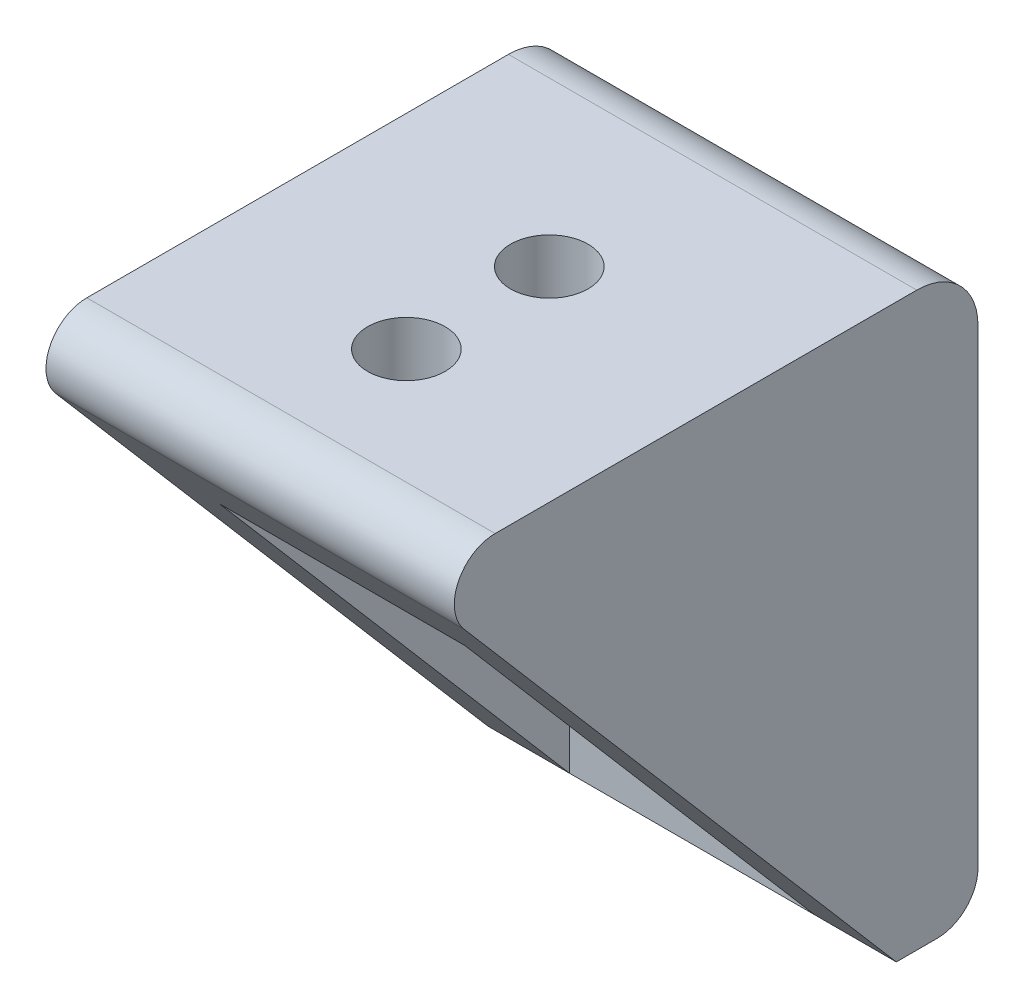
SolidWorks part; units mm, degrees
ref_plane "Front Plane" through (0, 0, 0) normal (0, 0, 1) x (1, 0, 0)
ref_plane "Top Plane" through (0, 0, 0) normal (0, 1, 0) x (1, 0, 0)
ref_plane "Right Plane" through (0, 0, 0) normal (1, 0, 0) x (0, 0, -1)
sketch "Sketch1" plane through (0, 0, 0) normal (0, 0, 1) x (1, 0, 0)
  line L1 (-10, -14) -> (10, -14)
  line L2 (-10, -14) -> (-10, 14)
  line L3 (-10, 14) -> (10, 14)
  line L4 (10, -14) -> (10, 14)
  line L5 (-10, -14) -> (10, 14) construction
  line L6 (-10, 14) -> (10, -14) construction
  point P0 (0, 0)
  dimension "D1" = 20
  dimension "D2" = 28
extrude "Boss-Extrude1" add sketch "Sketch1" along normal blind 28
ref_plane "Plane1" through (0, 0, 0) normal (-1, 0, 0) x (0, 0, 1)
sketch "Sketch2" plane through (0, 0, 0) normal (-1, 0, 0) x (0, 0, 1)
  line L1 (4, 6) -> (28, 6)
  line L2 (4, 6) -> (4, -14)
  line L3 (4, -14) -> (28, -14)
  line L4 (28, 6) -> (28, -14)
  line L5 (0, 14) -> (0, -14) construction
  line L6 (28, 14) -> (0, 14) construction
  line L7 (28, -14) -> (0, -14) construction
  line L8 (28, 14) -> (28, -14) construction
  dimension "D1" = 4
  dimension "D2" = 8
extrude "Cut-Extrude1" cut sketch "Sketch2" against normal offset from surface 4 and the other way offset from surface (6 mm away) 4 up to face at (10, 0, 14) other way up to face at (-10, 0, 14)
sketch "Sketch3" plane through (-10, 0, 0) normal (-1, 0, 0) x (0, 0, 1)
  line L0 (28, 14) -> (4, -14)
  line L1 (28, 14) -> (28, -14)
  line L2 (28, -14) -> (0, -14) construction
  line L3 (4, -14) -> (28, -14)
extrude "Cut-Extrude2" cut sketch "Sketch3" against normal up to surface (20 mm away) up to face at (10, 0, 14)
fillet "Fillet1" radius 2 1 edges at (0, 14, 28)
sketch "Sketch4" plane through (0, 14, 0) normal (0, 1, 0) x (1, 0, 0)
  line L1 (0, 0) -> (0, -23.6516) construction
  line L2 (10, 0) -> (-10, 0) construction
  line L3 (-10, -23.6516) -> (10, -23.6516) construction
  arc A0 (-1.75, -9.3) -> (1.75, -9.3) centre (0, -9.3) ccw construction
  arc A1 (1.75, -9.3) -> (-1.75, -9.3) centre (0, -9.3) ccw construction
  arc A2 (-1.75, -9.3) -> (1.75, -9.3) centre (0, -9.3) ccw construction
  arc A3 (1.75, -9.3) -> (-1.75, -9.3) centre (0, -9.3) ccw construction
  arc A4 (-1.75, -16.3) -> (1.75, -16.3) centre (0, -16.3) ccw construction
  arc A5 (1.75, -16.3) -> (-1.75, -16.3) centre (0, -16.3) ccw construction
  arc A6 (-1.75, -16.3) -> (1.75, -16.3) centre (0, -16.3) ccw construction
  arc A7 (1.75, -16.3) -> (-1.75, -16.3) centre (0, -16.3) ccw construction
  circle A10 centre (0, -11) radius 1.9
  circle A11 centre (0, -18) radius 1.9
  dimension "D1" = 3.8
  dimension "D4" = 3.8
  dimension "D2" = 11
  dimension "D3" = 7
extrude "Cut-Extrude3" cut sketch "Sketch4" against normal blind 10
sketch "Sketch5" plane through (0, 0, 4) normal (0, 0, 1) x (1, 0, 0)
  line L0 (0, 6) -> (0, -14) construction
  line L1 (6, 6) -> (-6, 6) construction
  line L2 (6, -14) -> (-6, -14) construction
  circle A0 centre (0, -2) radius 1.9
  circle A1 centre (0, -10) radius 1.9
  dimension "D4" = 3.8
  dimension "D3" = 3.8
  dimension "D1" = 8
  dimension "D2" = 4
extrude "Cut-Extrude4" cut sketch "Sketch5" against normal through all
fillet "Fillet2" radius 2 1 edges at (0, -14, 0)
fillet "Fillet3" radius 3 1 edges at (0, 14, 0)
equation "\"D4@Sketch4\"=\"D1@Sketch4\""
equation "\"D4@Sketch5\"=\"D3@Sketch5\""
